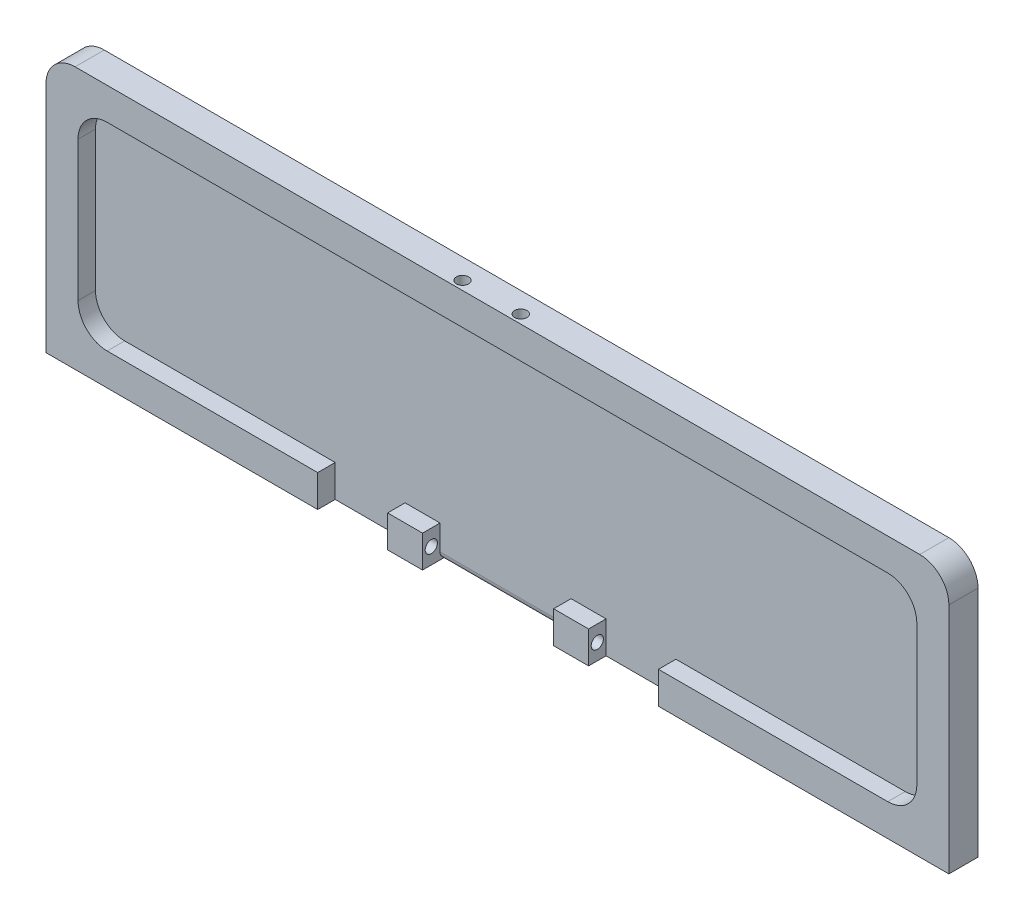
SolidWorks part; units mm, degrees
ref_plane "前视基准面" through (0, 0, 0) normal (0, 0, 1) x (1, 0, 0)
ref_plane "上视基准面" through (0, 0, 0) normal (0, 1, 0) x (1, 0, 0)
ref_plane "右视基准面" through (0, 0, 0) normal (1, 0, 0) x (0, 0, -1)
sketch "草图1" plane through (0, 0, 0) normal (0, 0, 1) x (1, 0, 0)
  line L1 (77.5, -22.5) -> (-77.5, -22.5)
  line L2 (77.5, -22.5) -> (77.5, 22.5)
  line L3 (77.5, 22.5) -> (-77.5, 22.5)
  line L4 (-77.5, -22.5) -> (-77.5, 22.5)
  line L5 (77.5, -22.5) -> (-77.5, 22.5) construction
  line L6 (77.5, 22.5) -> (-77.5, -22.5) construction
  point P0 (0, 0)
  dimension "D1" = 155
  dimension "D2" = 45
extrude "凸台-拉伸1" add sketch "草图1" along normal blind 5
sketch "草图2" plane through (0, 0, 5) normal (0, 0, 1) x (1, 0, 0)
  line L0 (77.5, 22.5) -> (-77.5, 22.5) construction
  line L1 (72, -17) -> (-72, -17)
  line L2 (72, -17) -> (72, 17)
  line L3 (72, 17) -> (-72, 17)
  line L4 (-72, -17) -> (-72, 17)
  line L5 (72, -17) -> (-72, 17) construction
  line L6 (72, 17) -> (-72, -17) construction
  line L7 (-77.5, 22.5) -> (-77.5, -22.5) construction
  point P0 (0, 0)
  dimension "D1" = 5.5
  dimension "D2" = 5.5
extrude "切除-拉伸1" cut sketch "草图2" against normal blind 3
fillet "圆角1" radius 5 2 edges at (77.5, 22.5, 2.5) (-77.5, 22.5, 2.5)
fillet "圆角2" radius 5 4 edges at (-72, 17, 3.5) (-72, -17, 3.5) (72, -17, 3.5) (72, 17, 3.5)
sketch "草图7" plane through (0, 0, 5) normal (0, 0, 1) x (1, 0, 0)
  line L0 (9.6457, -17) -> (9.6457, -22.5)
  line L1 (-67, -17) -> (67, -17) construction
  line L2 (-77.5, -22.5) -> (77.5, -22.5) construction
  line L3 (9.6457, -22.5) -> (-12.8543, -22.5)
  line L4 (-12.8543, -22.5) -> (-12.8543, -17)
  line L5 (-12.8543, -17) -> (9.6457, -17)
  line L6 (9.1457, 5.15) -> (9.1457, -23.5) construction
  line L7 (-12.3543, -23.5) -> (-12.3543, 5.15) construction
  dimension "D1" = 0.5
  dimension "D2" = 0.5
extrude "切除-拉伸2" cut sketch "草图7" against normal blind 3
fillet "圆角7" radius 1.2 1 edges at (-1.6043, -22.5, 2)
sketch "草图9" plane through (0, 0, 5) normal (0, 0, 1) x (1, 0, 0)
  line L0 (15.6457, -22.5) -> (15.6457, -17)
  line L1 (9.6457, -22.5) -> (77.5, -22.5) construction
  line L2 (9.6457, -17) -> (67, -17) construction
  line L3 (15.6457, -17) -> (27.6457, -17)
  line L4 (27.6457, -17) -> (27.6457, -22.5)
  line L5 (27.6457, -22.5) -> (15.6457, -22.5)
  line L6 (9.6457, -22.5) -> (9.6457, -17) construction
  dimension "D1" = 6
  dimension "D2" = 12
extrude "切除-拉伸3" cut sketch "草图9" against normal blind 3
hole_wizard "Ø2.1 (2.1) 直径孔1" positions "草图12" profile "草图11" hole size "Ø2.1" standard "GB"
sketch "草图12" plane through (15.6457, 0, 0) normal (1, 0, 0) x (0, 0, -1)
  line L0 (-5, -22.5) -> (-2, -17) construction
  line L2 (-2, -22.5) -> (-5, -17) construction
  point P0 (-3.5, -19.75)
sketch "草图11" plane through (15.6457, -19.75, 3.5) normal (0, 1, 0) x (0, 0, -1)
  line L0 (0, 0) -> (0, 36.6309)
  line L1 (0, 36.6309) -> (1.05, 36)
  line L2 (1.05, 36) -> (1.05, 0)
  line L5 (1.05, 0) -> (0, 0)
  line L10 (0, 36.6309) -> (-1.05, 36) construction
  line L11 (0, -6.35) -> (0, 107.95) construction
  dimension "孔直径" = 2.1
  dimension "孔深度" = 36
  dimension "导头角度" = 118
hole_wizard "Ø2.1 (2.1) 直径孔2" positions "草图13" profile "草图14" hole size "Ø2.1" standard "GB"
sketch "草图13" plane through (0, 22.5, 0) normal (0, 1, 0) x (1, 0, 0)
  line L0 (72.5, -5) -> (-72.5, -5) construction
  point P0 (2.5, -3.5)
  point P2 (-7.5, -3.5)
  dimension "D1" = 10
  dimension "D2" = 2.5
  dimension "D3" = 1.5
sketch "草图14" plane through (2.5, 22.5, 3.5) normal (1, 0, 0) x (0, 0, 1)
  line L0 (0, 0) -> (0, 13.8309)
  line L1 (0, 13.8309) -> (1.05, 13.2)
  line L2 (1.05, 13.2) -> (1.05, 0)
  line L5 (1.05, 0) -> (0, 0)
  line L10 (0, 13.8309) -> (-1.05, 13.2) construction
  line L11 (0, -6.35) -> (0, 107.95) construction
  dimension "孔直径" = 2.1
  dimension "孔深度" = 13.2
  dimension "导头角度" = 118
sketch "草图15" plane through (0, 0, 5) normal (0, 0, 1) x (1, 0, 0)
  line L0 (-18.8543, -22.5) -> (-18.8543, -17)
  line L1 (-77.5, -22.5) -> (-12.8543, -22.5) construction
  line L2 (-67, -17) -> (-12.8543, -17) construction
  line L3 (-18.8543, -17) -> (-30.8543, -17)
  line L4 (-30.8543, -17) -> (-30.8543, -22.5)
  line L5 (-30.8543, -22.5) -> (-18.8543, -22.5)
  line L6 (-12.8543, -17) -> (-12.8543, -22.5) construction
  dimension "D1" = 6
  dimension "D2" = 12
extrude "切除-拉伸4" cut sketch "草图15" against normal up to surface (3 mm away) up to face at (5.0104, -9.725, 2)
